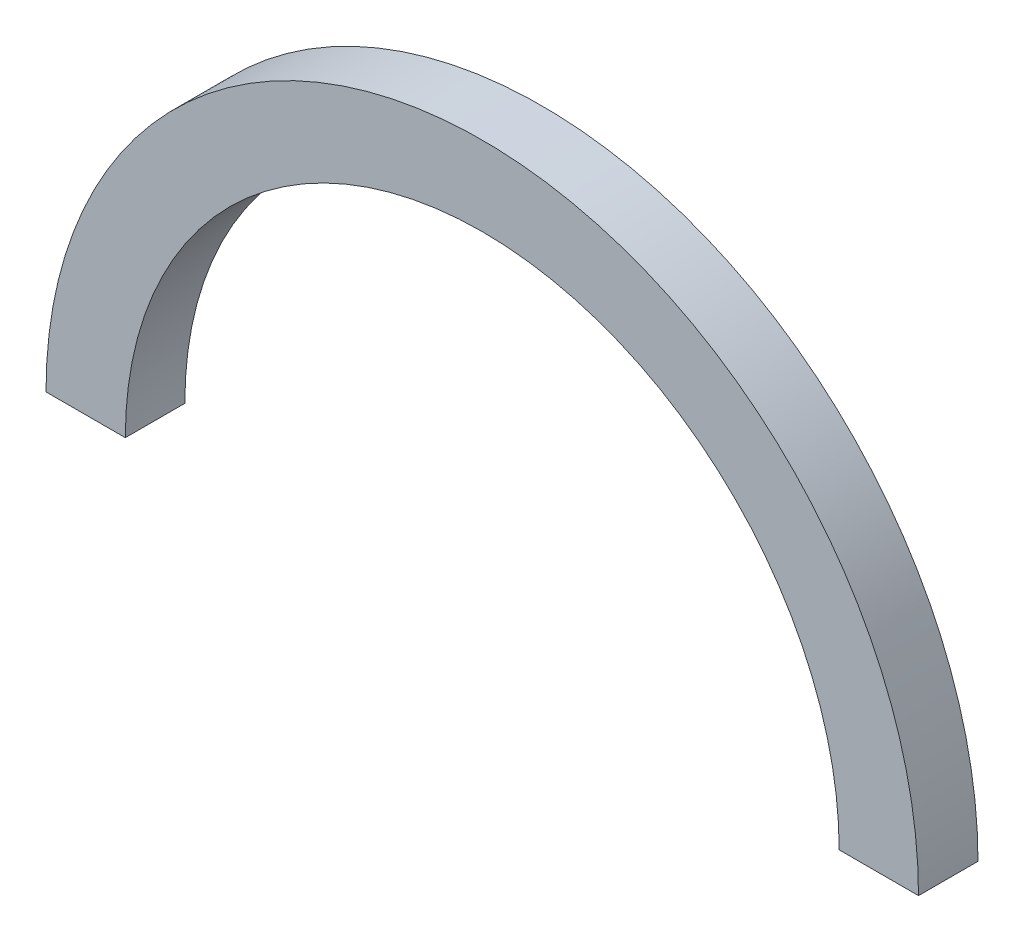
SolidWorks part; units mm, degrees
ref_plane "Plan de face" through (0, 0, 0) normal (0, 0, 1) x (1, 0, 0)
ref_plane "Plan de dessus" through (0, 0, 0) normal (0, 1, 0) x (1, 0, 0)
ref_plane "Plan de droite" through (0, 0, 0) normal (1, 0, 0) x (0, 0, -1)
sketch "Esquisse3" plane through (0, 0, 0) normal (0, 1, 0) x (1, 0, 0)
  line L1 (2395.772, 6775.6217) -> (2595.772, 6775.6217)
  line L2 (2395.772, 6775.6217) -> (2395.772, 6625.6217)
  line L3 (2395.772, 6625.6217) -> (2595.772, 6625.6217)
  line L4 (2595.772, 6775.6217) -> (2595.772, 6625.6217)
  line L5 (2395.772, 6775.6217) -> (2595.772, 6625.6217) construction
  line L6 (2395.772, 6625.6217) -> (2595.772, 6775.6217) construction
  point P0 (2495.772, 6700.6217)
  point P5 (0, 0)
  dimension "D1" = 200
  dimension "D2" = 150
sketch "Esquisse5" plane through (0, 0, -6700.6217) normal (0, 0, 1) x (1, 0, 0)
  line L0 (3495.772, 0) -> (2495.772, 0) construction
  arc A0 (2495.772, 0) -> (4495.772, 0) centre (3495.772, 0) cw
  point P4 (0, 0)
  dimension "D1" = 1000
sweep "Balayage3" add profiles "Esquisse3" path "Esquisse5"
